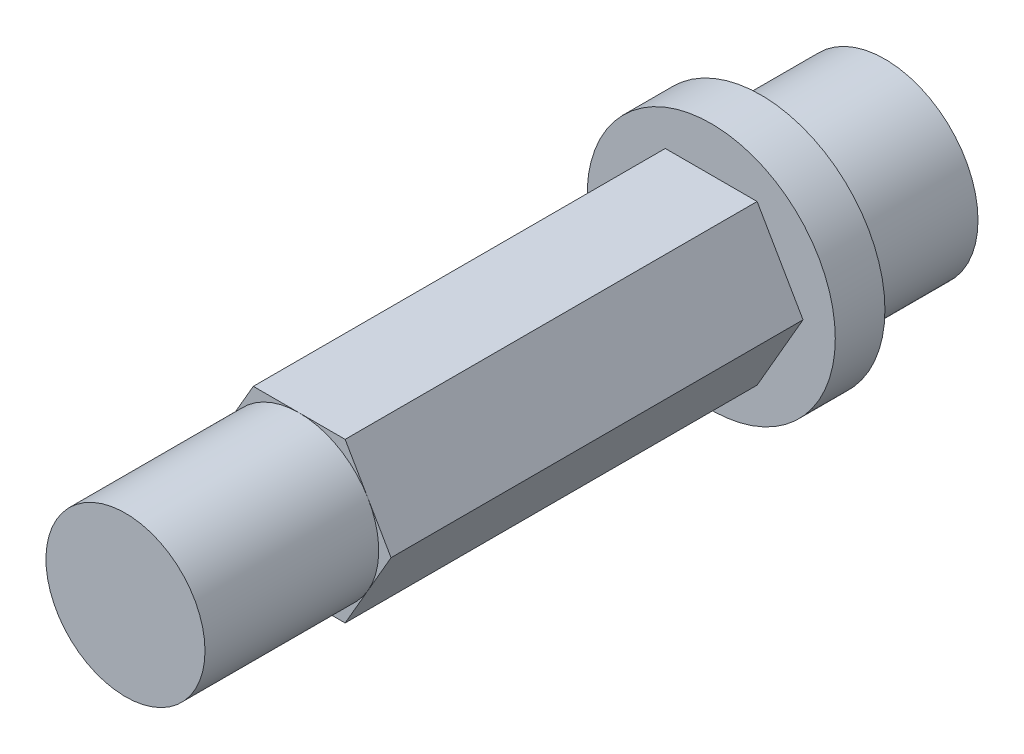
SolidWorks part; units mm, degrees
ref_plane "Front Plane" through (0, 0, 0) normal (0, 0, 1) x (1, 0, 0)
ref_plane "Top Plane" through (0, 0, 0) normal (0, 1, 0) x (1, 0, 0)
ref_plane "Right Plane" through (0, 0, 0) normal (1, 0, 0) x (0, 0, -1)
sketch "Sketch1" plane through (0, 0, 0) normal (0, 0, 1) x (1, 0, 0)
  circle A0 centre (0, 0) radius 3.75
  dimension "D1" = 7.5
extrude "Boss-Extrude1" add sketch "Sketch1" along normal blind 5
sketch "Sketch2" plane through (0, 0, 5) normal (0, 0, 1) x (1, 0, 0)
  circle A0 centre (0, 0) radius 5
  dimension "D1" = 10
extrude "Boss-Extrude2" add sketch "Sketch2" along normal blind 2
sketch "Sketch3" plane through (0, 0, 7) normal (0, 0, 1) x (1, 0, 0)
  line L7 (3.7, 0) -> (1.85, 3.2043)
  line L8 (1.85, 3.2043) -> (-1.85, 3.2043)
  line L9 (-1.85, 3.2043) -> (-3.7, 0)
  line L10 (-3.7, 0) -> (-1.85, -3.2043)
  line L11 (-1.85, -3.2043) -> (1.85, -3.2043)
  line L12 (1.85, -3.2043) -> (3.7, 0)
  circle A0 centre (0, 0) radius 3.7 construction
  circle A1 centre (0, 0) radius 3.2043 construction
  dimension "D1" = 7.4
extrude "Boss-Extrude3" add sketch "Sketch3" along normal blind 16.6
sketch "Sketch4" plane through (0, 0, 23.6) normal (0, 0, 1) x (1, 0, 0)
  line L2 (-1.85, 3.2043) -> (-3.7, 0) construction
  circle A0 centre (0, 0) radius 3.2043
extrude "Boss-Extrude4" add sketch "Sketch4" along normal blind 7
equation "\"gear_length\"=16.6"
equation "\"D1@Boss-Extrude3\"=\"gear_length\""
